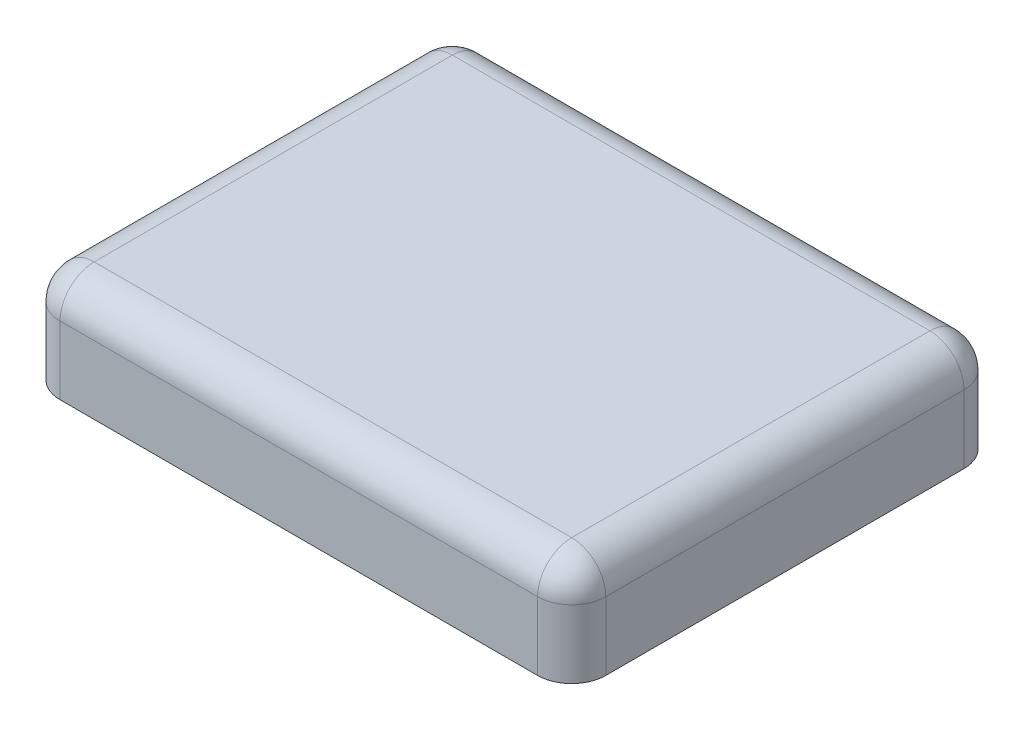
SolidWorks part; units mm, degrees
ref_plane "Front Plane" through (0, 0, 0) normal (0, 0, 1) x (1, 0, 0)
ref_plane "Top Plane" through (0, 0, 0) normal (0, 1, 0) x (1, 0, 0)
ref_plane "Right Plane" through (0, 0, 0) normal (1, 0, 0) x (0, 0, -1)
sketch "BaseS" plane through (0, 0, 0) normal (0, 1, 0) x (1, 0, 0)
  line L1 (-1.6, 1.25) -> (1.6, 1.25)
  line L2 (-1.6, 1.25) -> (-1.6, -1.25)
  line L3 (-1.6, -1.25) -> (1.6, -1.25)
  line L4 (1.6, 1.25) -> (1.6, -1.25)
  line L5 (-1.6, 1.25) -> (1.6, -1.25) construction
  line L6 (-1.6, -1.25) -> (1.6, 1.25) construction
  point P0 (0, 0)
  dimension "Width" = 3.2
  dimension "Length" = 2.5
extrude "Base" add sketch "BaseS" along normal blind 0.6
fillet "SideF" radius 0.2 4 edges at (1.6, 0.3, 1.25) (1.6, 0.3, -1.25) (-1.6, 0.3, 1.25) (-1.6, 0.3, -1.25)
fillet "TopF" radius 0.2 8 edges at (-1.5414, 0.6, 1.1914) (-1.6, 0.6, 0) (-1.5414, 0.6, -1.1914) (0, 0.6, -1.25) (1.5414, 0.6, -1.1914) (1.6, 0.6, 0) (1.5414, 0.6, 1.1914) (0, 0.6, 1.25)
